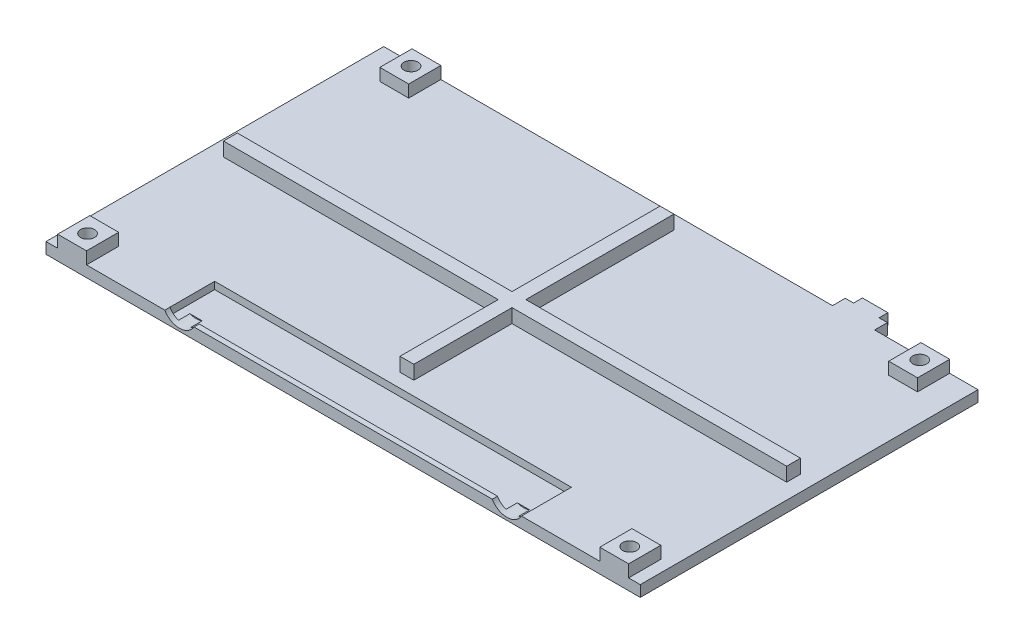
SolidWorks part; units mm, degrees
ref_plane "Front Plane" through (0, 0, 0) normal (0, 0, 1) x (1, 0, 0)
ref_plane "Top Plane" through (0, 0, 0) normal (0, 1, 0) x (1, 0, 0)
ref_plane "Right Plane" through (0, 0, 0) normal (1, 0, 0) x (0, 0, -1)
sketch "Sketch1" plane through (0, 0, 0) normal (0, 1, 0) x (1, 0, 0)
  line L1 (0, 0) -> (136.0932, 0)
  line L2 (0, 0) -> (0, 77.343)
  line L3 (0, 77.343) -> (136.0932, 77.343)
  line L4 (136.0932, 0) -> (136.0932, 77.343)
  dimension "D1" = 77.343
  dimension "D2" = 136.0932
extrude "Boss-Extrude1" add sketch "Sketch1" along normal blind 2.54
sketch "Sketch2" plane through (0, 0, 0) normal (0, 0, 1) x (1, 0, 0)
  line L0 (68.0466, 0) -> (68.0466, -15.1039) construction
  line L1 (0, 0) -> (136.0932, 0) construction
  circle A0 centre (105.5477, 4.4939) radius 3.8735
  arc A1 (102.157, 5.3311) -> (102.6529, 2.54) centre (105.5477, 4.4939) ccw construction
  circle A2 centre (30.5455, 4.4939) radius 3.8735
  dimension "D1" = 0.381
extrude "Cut-Extrude1" cut sketch "Sketch2" against normal blind 3.81
sketch "Sketch3" plane through (0, 2.54, 0) normal (0, 1, 0) x (1, 0, 0)
  line L0 (33.8901, 0) -> (102.2031, 0) construction
  line L1 (27.2009, 11.43) -> (108.8923, 11.43)
  line L2 (27.2009, 11.43) -> (27.2009, 1.1938)
  line L3 (27.2009, 1.1938) -> (108.8923, 1.1938)
  line L4 (108.8923, 11.43) -> (108.8923, 1.1938)
  line L5 (27.2009, 1.905) -> (27.2009, -5.0299) construction
  line L6 (27.2009, 0) -> (27.2009, 3.81) construction
  line L7 (108.8923, 0.5023) -> (108.8923, -8.1174) construction
  line L8 (108.8923, 3.81) -> (108.8923, 0) construction
  dimension "D1" = 1.1938
  dimension "D3" = 11.43
extrude "Cut-Extrude2" cut sketch "Sketch3" against normal blind 1.651
sketch "Sketch4" plane through (0, 2.54, 0) normal (0, 1, 0) x (1, 0, 0)
  line L0 (108.8923, 0) -> (136.0932, 0) construction
  line L1 (133.4262, 0) -> (126.8222, 0)
  line L2 (133.4262, 0) -> (133.4262, 7.366)
  line L3 (133.4262, 7.366) -> (126.8222, 7.366)
  line L4 (126.8222, 0) -> (126.8222, 7.366)
  line L5 (133.8072, 7.366) -> (124.9172, 7.366) construction
  line L6 (133.8072, 69.977) -> (133.8072, -0.254) construction
  line L7 (126.4412, 2.286) -> (126.4412, -0.254) construction
  line L8 (68.0466, 0) -> (68.0466, 77.343) construction
  line L9 (33.8901, 0) -> (102.2031, 0) construction
  line L10 (136.0932, 77.343) -> (0, 77.343) construction
  line L11 (9.271, 0) -> (9.271, 7.366)
  line L12 (2.667, 7.366) -> (9.271, 7.366)
  line L13 (2.667, 0) -> (2.667, 7.366)
  line L14 (2.667, 0) -> (9.271, 0)
  line L15 (119.8372, 69.977) -> (129.9972, 69.977) construction
  line L16 (129.6162, 69.977) -> (123.0122, 69.977)
  line L17 (129.6162, 69.977) -> (129.6162, 77.343)
  line L18 (129.6162, 77.343) -> (123.0122, 77.343)
  line L19 (123.0122, 69.977) -> (123.0122, 77.343)
  line L20 (129.9972, 71.247) -> (129.9972, 77.597) construction
  line L21 (122.6312, 72.517) -> (122.6312, 77.597) construction
  line L22 (13.081, 69.977) -> (13.081, 77.343)
  line L23 (6.477, 77.343) -> (13.081, 77.343)
  line L24 (6.477, 69.977) -> (6.477, 77.343)
  line L25 (6.477, 69.977) -> (13.081, 69.977)
  dimension "D1" = 0.381
  dimension "D2" = 0.381
  dimension "D3" = 0.381
  dimension "D4" = 0.381
extrude "Boss-Extrude4" add sketch "Sketch4" along normal blind 2.794
sketch "Sketch5" plane through (0, 0, 0) normal (0, -1, 0) x (-1, 0, 0)
  circle A0 centre (-126.3142, 73.787) radius 2.8575
  circle A1 centre (-9.8044, 73.787) radius 2.8575
  circle A2 centre (-5.969, 3.556) radius 2.8575
  circle A3 centre (-130.1242, 3.556) radius 2.8575
  dimension "D1" = 5.715
  dimension "D2" = 5.715
  dimension "D3" = 5.715
  dimension "D4" = 5.715
extrude "Cut-Extrude3" cut sketch "Sketch5" against normal blind 2.032
hole_wizard "M3 Clearance Hole1" positions "Sketch8" profile "Sketch7" hole size "M3" standard "ANSI Metric" end condition through all
sketch "Sketch8" plane through (0, 2.032, 0) normal (0, -1, 0) x (-1, 0, 0)
  point P0 (-5.969, 3.556)
  point P2 (-130.1242, 3.556)
  point P4 (-126.3142, 73.787)
  point P6 (-9.8044, 73.787)
sketch "Sketch7" plane through (5.969, 2.032, -3.556) normal (1, 0, 0) x (0, 0, -1)
  line L0 (0, 0) -> (0, 3.302)
  line L1 (0, 3.302) -> (1.6, 3.302)
  line L2 (1.6, 3.302) -> (1.6, 0)
  line L5 (1.6, 0) -> (0, 0)
  line L11 (0, -6.35) -> (0, 107.95) construction
  dimension "Thru Hole Dia." = 3.2
  dimension "Thru Hole Depth" = 3.302
sketch "Sketch9" plane through (0, 0, -77.343) normal (0, 0, -1) x (-1, 0, 0)
  line L0 (-136.0932, 0) -> (0, 0) construction
  line L1 (-102.7684, 0) -> (-112.4204, 0)
  line L2 (-102.7684, 0) -> (-102.7684, 2.54)
  line L3 (-102.7684, 2.54) -> (-112.4204, 2.54)
  line L4 (-112.4204, 0) -> (-112.4204, 2.54)
  line L5 (-123.0122, 2.54) -> (-13.081, 2.54) construction
  line L6 (-136.0932, 2.54) -> (-136.0932, 0) construction
  dimension "D1" = 23.6728
  dimension "D2" = 9.652
extrude "Boss-Extrude5" add sketch "Sketch9" along normal blind 2.921
sketch "Sketch10" plane through (0, 0, -80.264) normal (0, 0, -1) x (-1, 0, 0)
  line L0 (-112.4204, 0) -> (-102.7684, 0) construction
  line L1 (-104.6734, 0) -> (-110.5154, 0)
  line L2 (-104.6734, 0) -> (-104.6734, 2.54)
  line L3 (-104.6734, 2.54) -> (-110.5154, 2.54)
  line L4 (-110.5154, 0) -> (-110.5154, 2.54)
  line L5 (-102.7684, 2.54) -> (-112.4204, 2.54) construction
  line L6 (-107.5944, 0) -> (-107.5944, -5.4629) construction
  point P10 (-107.5944, 0)
  dimension "D1" = 5.842
extrude "Boss-Extrude6" add sketch "Sketch10" along normal blind 2.032
sketch "Sketch11" plane through (0, 2.54, 0) normal (0, 1, 0) x (1, 0, 0)
  line L0 (132.5372, 37.084) -> (69.6341, 37.084)
  line L1 (69.6341, 37.084) -> (69.6341, 14.605)
  line L2 (69.6341, 14.605) -> (66.4591, 14.605)
  line L3 (66.4591, 14.605) -> (66.4591, 37.084)
  line L4 (66.4591, 37.084) -> (3.556, 37.084)
  line L5 (3.556, 37.084) -> (3.556, 40.259)
  line L6 (3.556, 40.259) -> (66.4591, 40.259)
  line L7 (66.4591, 40.259) -> (66.4591, 74.168)
  line L8 (66.4591, 74.168) -> (69.6341, 74.168)
  line L9 (69.6341, 74.168) -> (69.6341, 40.259)
  line L10 (69.6341, 40.259) -> (132.5372, 40.259)
  line L11 (132.5372, 40.259) -> (132.5372, 37.084)
  line L12 (119.5944, 0) -> (119.5944, 77.343) construction
  line L13 (108.8923, 0) -> (126.8222, 0) construction
  line L14 (136.0932, 26.1452) -> (0, 26.1452) construction
  line L15 (136.0932, 0) -> (136.0932, 77.343) construction
  line L16 (68.0466, 26.1452) -> (68.0466, 136.8054) construction
  line L17 (119.5944, 38.6715) -> (-20.0982, 38.6715) construction
  line L18 (133.8072, 69.977) -> (133.8072, -0.254) construction
  line L19 (2.286, 69.977) -> (2.286, -0.254) construction
  line L20 (102.5144, 75.057) -> (16.2814, 75.057) construction
  line L21 (108.8923, 11.43) -> (27.2009, 11.43) construction
  line L22 (0, 77.343) -> (0, 0) construction
  line L23 (123.0122, 77.343) -> (112.4204, 77.343) construction
  point P24 (132.5372, 38.6715)
  point P25 (68.0466, 14.605)
  point P34 (6.0756, 26.1667)
  point P35 (0, 26.1452)
  point P38 (119.5944, 77.343)
  dimension "D1" = 3.175
  dimension "D2" = 3.175
  dimension "D3" = 1.27
  dimension "D4" = 1.27
  dimension "D5" = 0.889
  dimension "D6" = 3.175
extrude "Boss-Extrude7" add sketch "Sketch11" along normal blind 3.175
